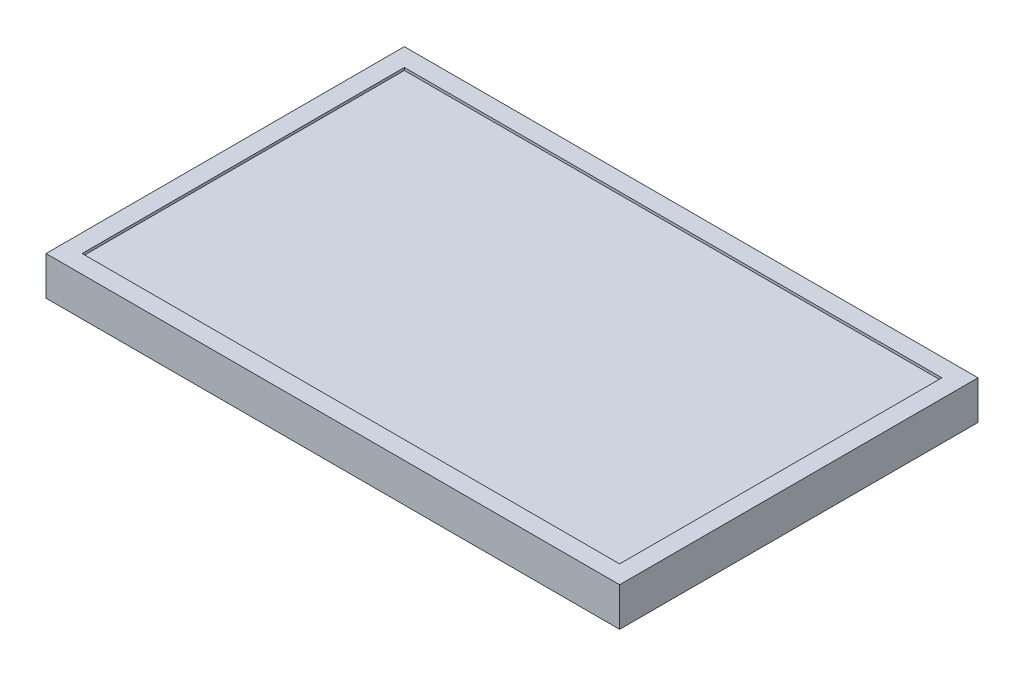
SolidWorks part; units mm, degrees
ref_plane "前基準面" through (0, 0, 0) normal (0, 0, 1) x (1, 0, 0)
ref_plane "上基準面" through (0, 0, 0) normal (0, 1, 0) x (1, 0, 0)
ref_plane "右基準面" through (0, 0, 0) normal (1, 0, 0) x (0, 0, -1)
sketch "草圖1" plane through (0, 0, 0) normal (0, 1, 0) x (1, 0, 0)
  line L1 (-222.5, -139) -> (222.5, -139)
  line L2 (-222.5, -139) -> (-222.5, 139)
  line L3 (-222.5, 139) -> (222.5, 139)
  line L4 (222.5, -139) -> (222.5, 139)
  line L5 (-222.5, -139) -> (222.5, 139) construction
  line L6 (-222.5, 139) -> (222.5, -139) construction
  point P0 (0, 0)
  dimension "D1" = 445
  dimension "D2" = 278
extrude "填料-伸長1" add sketch "草圖1" along normal blind 30
sketch "草圖2" plane through (0, 30, 0) normal (0, 1, 0) x (1, 0, 0)
  line L8 (208.5, -125) -> (208.5, 125)
  line L9 (208.5, 125) -> (-208.5, 125)
  line L10 (-208.5, 125) -> (-208.5, -125)
  line L11 (-208.5, -125) -> (208.5, -125)
  line L12 (208.5, -125) -> (208.5, 125)
  line L13 (208.5, 125) -> (-208.5, 125)
  line L14 (-208.5, 125) -> (-208.5, -125)
  line L15 (-208.5, -125) -> (208.5, -125)
  dimension "D1" = 14
extrude "除料-伸長1" cut sketch "草圖2" against normal blind 2
